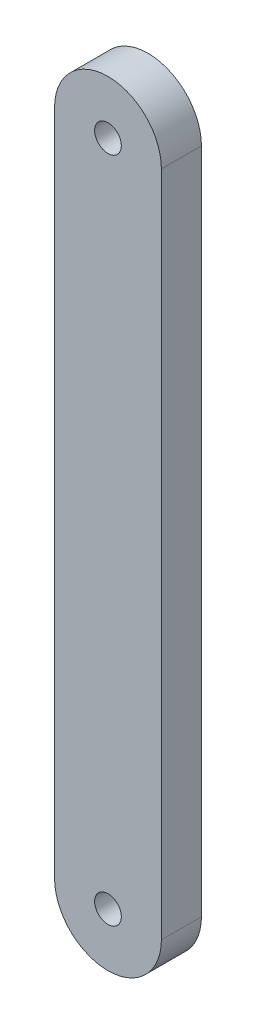
SolidWorks part; units mm, degrees
ref_plane "Front Plane" through (0, 0, 0) normal (0, 0, 1) x (1, 0, 0)
ref_plane "Top Plane" through (0, 0, 0) normal (0, 1, 0) x (1, 0, 0)
ref_plane "Right Plane" through (0, 0, 0) normal (1, 0, 0) x (0, 0, -1)
sketch "Model" plane through (0, 0, 0) normal (0, 0, 1) x (1, 0, 0)
  line L0 (34.7469, 62.5456) -> (34.7469, 12.5456)
  line L1 (42.7469, 62.5456) -> (42.7469, 12.5456)
  arc A0 (34.7469, 12.5456) -> (42.7469, 12.5456) centre (38.7469, 12.5456) ccw
  arc A1 (42.7469, 62.5456) -> (34.7469, 62.5456) centre (38.7469, 62.5456) ccw
  circle A2 centre (38.7469, 12.5456) radius 1
  circle A3 centre (38.7469, 62.5456) radius 1
extrude "Boss-Extrude1" add sketch "Model" along normal blind 3 contours A2 | A3 | L0 A0 L1 A1
